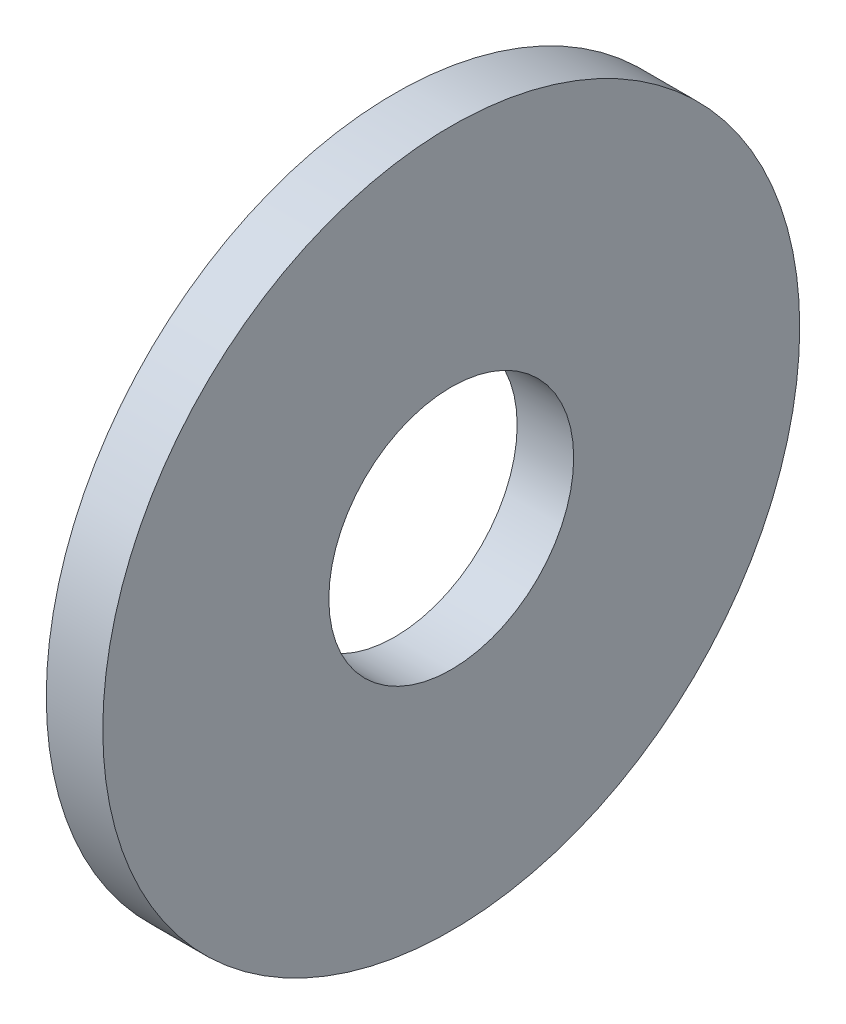
SolidWorks part; units mm, degrees
ref_plane "Plane1" through (0, 0, 0) normal (0, 0, 1) x (1, 0, 0)
ref_plane "Plane2" through (0, 0, 0) normal (0, 1, 0) x (1, 0, 0)
ref_plane "Plane3" through (0, 0, 0) normal (1, 0, 0) x (0, 0, -1)
revolve "Base-Revolve" add sketch "Sketch1" angle 360 about L0
sketch "Sketch1" plane through (0, 0, 0) normal (0, 0, 1) x (1, 0, 0)
  line L0 (-34.925, 0) -> (9.525, 0) construction
  line L1 (0, 6.5) -> (0, 18.5)
  line L2 (0, 18.5) -> (-3, 18.5)
  line L3 (-3, 18.5) -> (-3, 6.5)
  line L4 (-3, 6.5) -> (0, 6.5)
  dimension "Thickness" = 3
  dimension "Inside_dia" = 13
  dimension "Outside_dia" = 37
